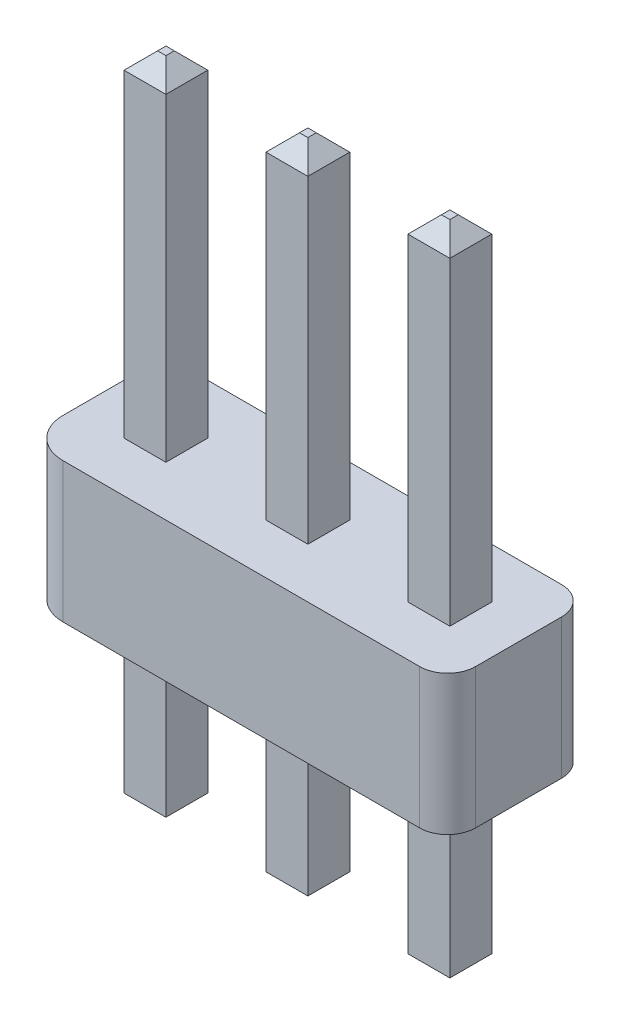
SolidWorks part; units mm, degrees
ref_plane "Front Plane" through (0, 0, 0) normal (0, 0, 1) x (1, 0, 0)
ref_plane "Top Plane" through (0, 0, 0) normal (0, 1, 0) x (1, 0, 0)
ref_plane "Right Plane" through (0, 0, 0) normal (1, 0, 0) x (0, 0, -1)
ref_plane "Plane1" through (0, 0, 0) normal (0, 1, 0) x (-1, 0, 0)
sketch "Sketch1" plane through (0, 0, 0) normal (0, 1, 0) x (-1, 0, 0)
  line L0 (-2, 1.27) -> (2, 1.27)
  line L1 (4.5452, 1.27) -> (5.0814, 1.27)
  line L2 (2, -1.27) -> (-2, -1.27)
  line L3 (-2.5, -0.77) -> (-2.5, 0.77)
  line L5 (55, 0) -> (-55, 0) construction
  line L6 (2, 1.27) -> (4.5452, 1.27)
  line L8 (4.5452, -1.27) -> (2, -1.27)
  line L9 (5.0814, 1.27) -> (5.0814, -1.27)
  line L10 (5.0814, -1.27) -> (4.5452, -1.27)
  arc A2 (-2.5, -0.77) -> (-2, -1.27) centre (-2, -0.77) ccw
  arc A3 (-2, 1.27) -> (-2.5, 0.77) centre (-2, 0.77) ccw
  dimension "D2" = 2.54
  dimension "D4" = 1.27
extrude "Boss-Extrude1" add sketch "Sketch1" along normal blind 2.5
ref_plane "Plane2" through (0, 0, 0) normal (0, 1, 0) x (-1, 0, 0)
sketch "Sketch2" plane through (0, 0, 0) normal (0, 1, 0) x (-1, 0, 0)
  line L0 (0.895, 0.375) -> (1.645, 0.375)
  line L1 (1.645, 0.375) -> (1.645, -0.375)
  line L2 (1.645, -0.375) -> (0.895, -0.375)
  line L3 (0.895, -0.375) -> (0.895, 0.375)
  line L4 (-0.895, -0.375) -> (-1.645, -0.375)
  line L5 (-1.645, -0.375) -> (-1.645, 0.375)
  line L6 (-1.645, 0.375) -> (-0.895, 0.375)
  line L7 (-0.895, 0.375) -> (-0.895, -0.375)
  line L8 (-1.645, 0.375) -> (-0.895, -0.375) construction
  line L9 (0.895, -0.375) -> (1.645, 0.375) construction
  line L10 (1.375, 0) -> (-1.375, 0) construction
  line L11 (0, 1.375) -> (0, -1.375) construction
  point P8 (-1.27, 0)
  point P9 (1.27, 0)
  dimension "D1" = 2.54
  dimension "D2" = 0.75
  dimension "D3" = 1.27
extrude "Boss-Extrude2" add sketch "Sketch2" along normal blind 8.5 and the other way blind 3.25
chamfer "Chamfer1" distance 0.3 angle 45 16 edges at (-1.645, 8.5, 0) (-1.27, 8.5, -0.375) (-0.895, 8.5, 0) (-1.27, 8.5, 0.375) (0.895, 8.5, 0) (1.27, 8.5, -0.375) (1.645, 8.5, 0) (1.27, 8.5, 0.375) (1.27, -3.25, -0.375) (1.645, -3.25, 0) (0.895, -3.25, 0) (1.27, -3.25, 0.375) (-1.27, -3.25, 0.375) (-1.645, -3.25, 0) (-0.895, -3.25, 0) (-1.27, -3.25, -0.375)
fillet "Redondeo3" radius 0.7 2 edges at (-5.0814, 1.25, 1.27) (-5.0814, 1.25, -1.27)
sketch "Croquis5" plane through (0, 2.5, 0) normal (0, 1, 0) x (1, 0, 0)
  line L0 (-0.895, 0.375) -> (-1.645, 0.375) construction
  line L1 (1.645, 0.375) -> (0.895, 0.375) construction
  line L2 (-0.895, 0.375) -> (-0.895, -0.375) construction
  line L3 (0.895, -0.375) -> (0.895, 0.375) construction
  line L4 (-1.645, -0.375) -> (-1.645, 0.375) construction
  line L9 (-3.435, 0.375) -> (-4.1835, 0.375)
  line L10 (-3.435, 0.375) -> (-3.435, -0.375)
  line L11 (-3.435, -0.375) -> (-4.1835, -0.375)
  line L12 (-4.1835, 0.375) -> (-4.1835, -0.375)
  line L13 (-3.435, 0.375) -> (-4.1835, -0.375) construction
  line L14 (-3.435, -0.375) -> (-4.1835, 0.375) construction
  point P8 (-3.8092, 0)
  point P18 (-1.645, 0)
  dimension "D1" = 1.79
extrude "Saliente-Extruir4" add sketch "Croquis5" along normal blind 5.7 and the other way blind 5.5
sketch "Croquis6" plane through (0, 8.2, 0) normal (0, 1, 0) x (1, 0, 0)
  line L0 (-4.1835, 0.375) -> (-4.1835, -0.375)
  line L1 (-4.1835, -0.375) -> (-3.435, -0.375)
  line L2 (-4.1835, -0.375) -> (-3.435, -0.375) construction
  line L3 (-4.1835, -0.375) -> (-3.435, -0.375) construction
  line L4 (-3.435, -0.375) -> (-3.435, 0.375)
  line L5 (-3.435, 0.375) -> (-4.1835, 0.375)
extrude "Saliente-Extruir5" add sketch "Croquis6" along normal blind 0.3 draft 45
sketch "Croquis7" plane through (0, -3, 0) normal (0, -1, 0) x (1, 0, 0)
  line L0 (-4.1835, -0.375) -> (-4.1835, 0.375)
  line L1 (-4.1835, 0.375) -> (-3.435, 0.375)
  line L2 (-3.435, 0.375) -> (-3.435, -0.375)
  line L3 (-3.435, -0.375) -> (-4.1835, -0.375)
extrude "Saliente-Extruir6" add sketch "Croquis7" along normal blind 0.3 draft 45
